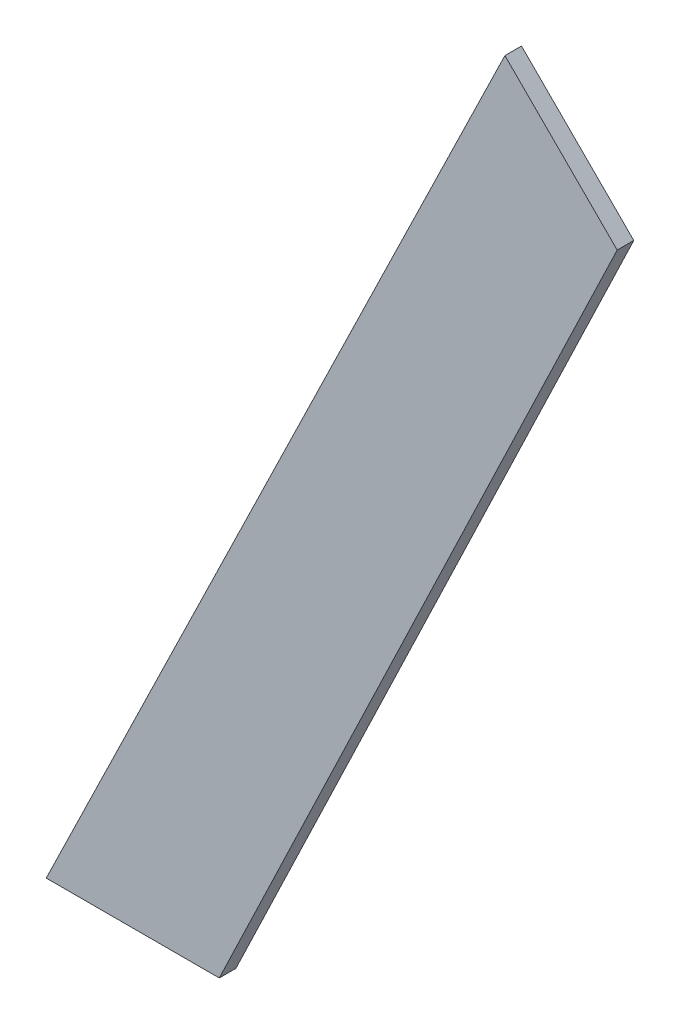
SolidWorks part; units mm, degrees
material "AISI 1020"
ref_plane "Front Plane" through (0, 0, 0) normal (0, 0, 1) x (1, 0, 0)
ref_plane "Top Plane" through (0, 0, 0) normal (0, 1, 0) x (1, 0, 0)
ref_plane "Right Plane" through (0, 0, 0) normal (1, 0, 0) x (0, 0, -1)
sketch "Sketch1" plane through (0, 0, 0) normal (0, 0, 1) x (1, 0, 0)
  line L1 (-158.4728, 20.8662) -> (-172.0098, 34.4033)
  line L12 (-172.0098, 34.4033) -> (-227.3155, -79.1338)
  line L13 (-227.3155, -79.1338) -> (-206.449, -79.1338)
  line L14 (-206.449, -79.1338) -> (-158.4728, 20.8662)
extrude "Boss-Extrude1" add sketch "Sketch1" against normal blind 2
